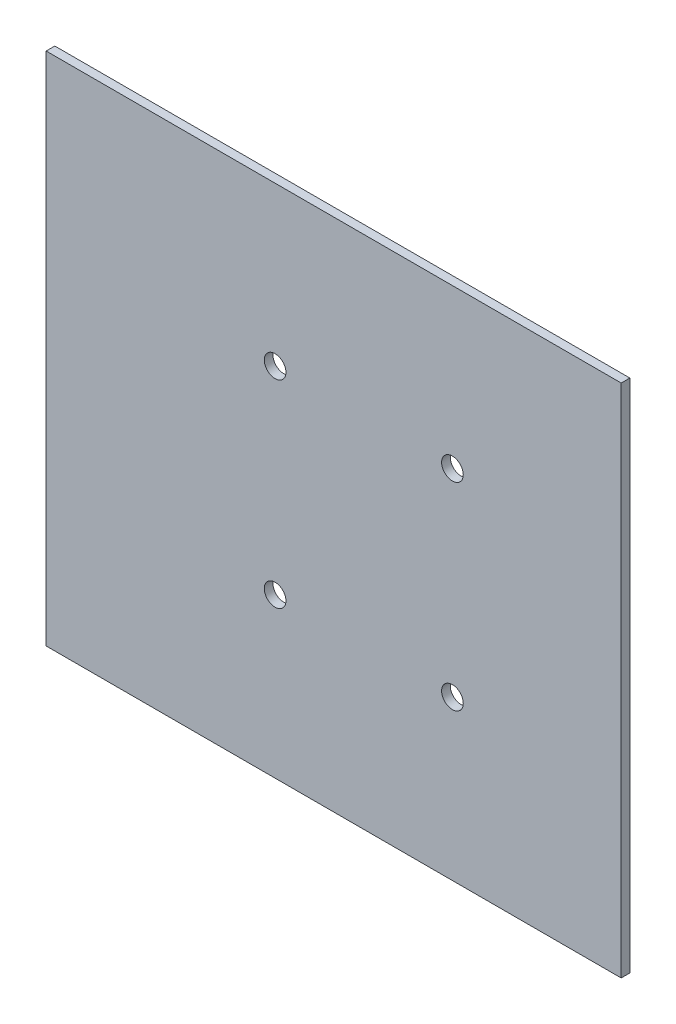
SolidWorks part; units mm, degrees
ref_plane "Plan de face" through (0, 0, 0) normal (0, 0, 1) x (1, 0, 0)
ref_plane "Plan de dessus" through (0, 0, 0) normal (0, 1, 0) x (1, 0, 0)
ref_plane "Plan de droite" through (0, 0, 0) normal (1, 0, 0) x (0, 0, -1)
sketch "Esquisse1" plane through (0, 0, 0) normal (0, 0, 1) x (1, 0, 0)
  line L1 (-49.1302, 219.1251) -> (229.7698, 219.1251)
  line L2 (-49.1302, 219.1251) -> (-49.1302, -30.7749)
  line L3 (-49.1302, -30.7749) -> (229.7698, -30.7749)
  line L4 (229.7698, 219.1251) -> (229.7698, -30.7749)
  dimension "D1" = 249.9
  dimension "D2" = 278.9
extrude "Boss.-Extru.1" add sketch "Esquisse1" along normal blind 4.2
sketch "Esquisse3" plane through (0, 0, 4.2) normal (0, 0, 1) x (1, 0, 0)
  line L0 (-49.1302, -30.7749) -> (229.7698, -30.7749) construction
  line L2 (-49.1302, 219.1251) -> (-49.1302, -30.7749) construction
  circle A0 centre (100.8698, 137.2251) radius 5.25
  circle A1 centre (100.8698, 51.2251) radius 5.25
  circle A2 centre (196.8698, 137.2251) radius 5.25
  circle A3 centre (196.8698, 51.2251) radius 5.25
  point P8 (0, 0)
  point P9 (0, 0)
  dimension "D5" = 10.5
  dimension "D6" = 10.5
  dimension "D7" = 10.5
  dimension "D8" = 10.5
  dimension "D1" = 96
  dimension "D2" = 96
  dimension "D3" = 86
  dimension "D4" = 86
  dimension "D9" = 82
  dimension "D10" = 150
sketch "Esquisse4" plane through (0, 0, 4.2) normal (0, 0, 1) x (1, 0, 0)
  circle A0 centre (61.9198, 142.2751) radius 5.25
  circle A1 centre (61.9198, 46.2751) radius 5.25
  circle A2 centre (147.9198, 142.2751) radius 5.25
  circle A3 centre (147.9198, 46.2751) radius 5.25
  dimension "D1" = 10.5
  dimension "D2" = 10.5
  dimension "D3" = 10.5
  dimension "D4" = 10.5
  dimension "D5" = 0
  dimension "D6" = 0
  dimension "D7" = 0
  dimension "D8" = 0
  dimension "D9" = 0
  dimension "D10" = 0
  dimension "D11" = 0
  dimension "D12" = 0
extrude "Enlèv. mat.-Extru.3" cut sketch "Esquisse4" against normal blind 5
